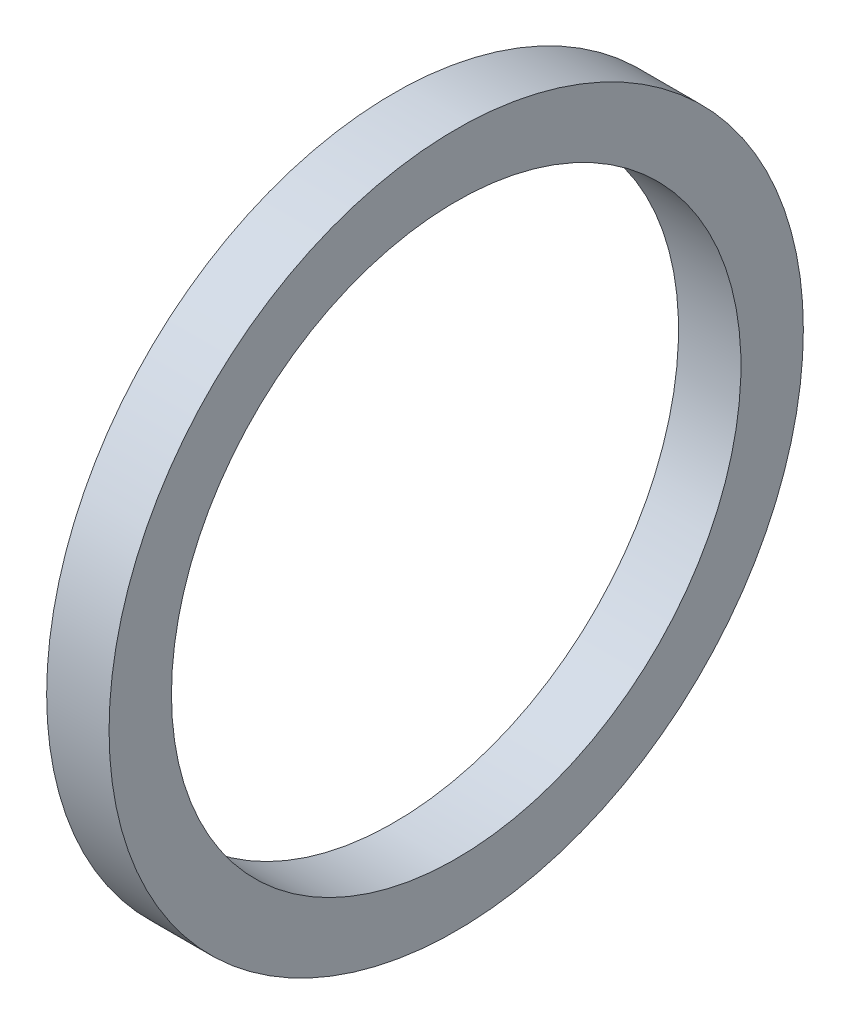
SolidWorks part; units mm, degrees
ref_plane "Front Plane" through (0, 0, 0) normal (0, 0, 1) x (1, 0, 0)
ref_plane "Top Plane" through (0, 0, 0) normal (0, 1, 0) x (1, 0, 0)
ref_plane "Right Plane" through (0, 0, 0) normal (1, 0, 0) x (0, 0, -1)
sketch "Sketch1" plane through (0, 0, 0) normal (0, 0, 1) x (1, 0, 0)
  line L0 (-43.7166, 0) -> (79.6876, 0) construction
  line L2 (0, -9.271) -> (2.032, -9.271)
  line L3 (0, -9.271) -> (0, -11.303)
  line L4 (0, -11.303) -> (2.032, -11.303)
  line L5 (2.032, -9.271) -> (2.032, -11.303)
  dimension "A" = 18.542
  dimension "B" = 22.606
  dimension "C" = 2.032
revolve "Revolve1" add sketch "Sketch1" angle 360 about L0
sketch "Sketch2" [suppressed] plane through (0, 0, 0) normal (0, 0, 1) x (1, 0, 0)
  line L0 (-34.685, 0) -> (47.6686, 0) construction
  circle A0 centre (2.54, -5.715) radius 0.762
  dimension "D1" = 2.54
  dimension "E" = 2.032
  dimension "D" = 12.954
revolve "Revolve3" [suppressed] add sketch "Sketch2" angle 360 about L0
